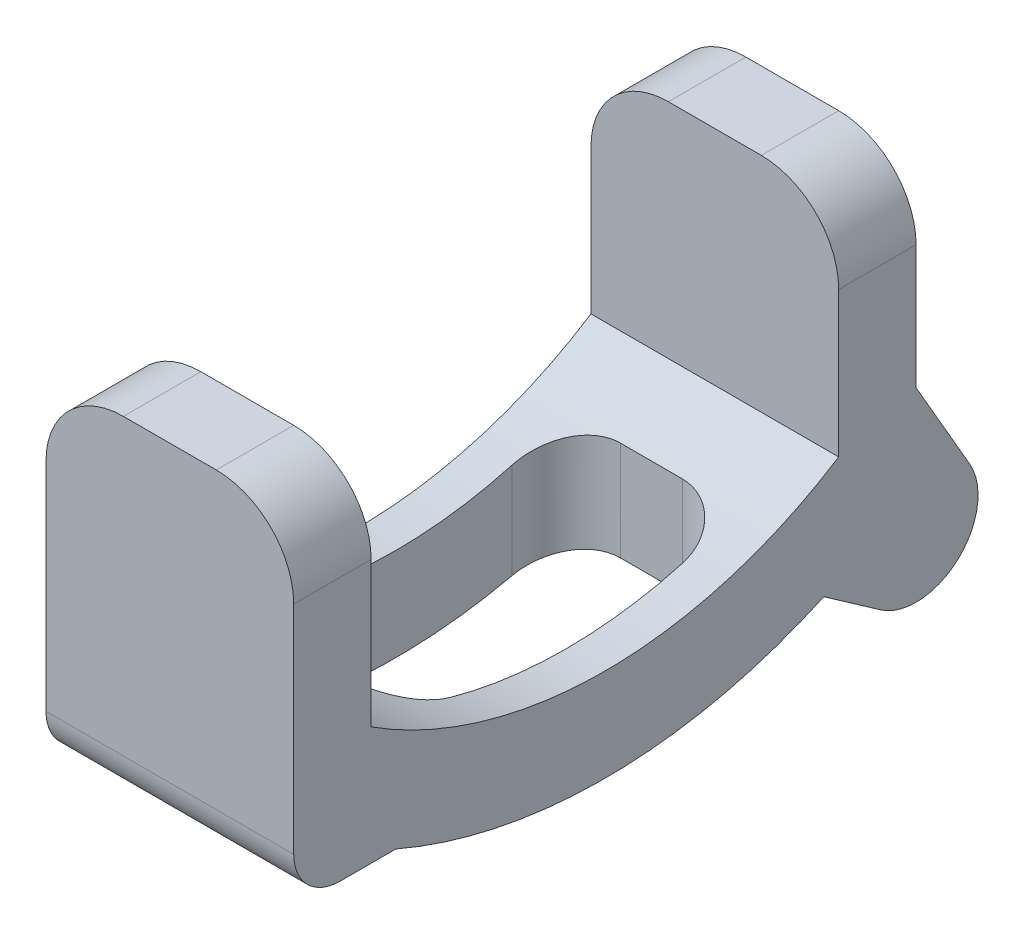
SolidWorks part; units mm, degrees
ref_plane "Přední rovina" through (0, 0, 0) normal (0, 0, 1) x (1, 0, 0)
ref_plane "Horní rovina" through (0, 0, 0) normal (0, 1, 0) x (1, 0, 0)
ref_plane "Pravá rovina" through (0, 0, 0) normal (1, 0, 0) x (0, 0, -1)
sketch "Skica1" plane through (0, 0, 0) normal (1, 0, 0) x (0, 0, -1)
  line L0 (-20.1, 0) -> (-20.1, 22)
  line L1 (-20.1, 22) -> (-15.1, 22)
  line L2 (-15.1, 22) -> (-15.1, 7.631)
  line L3 (0, 54.4876) -> (0, -54.4876) construction
  line L4 (-20.1, 0) -> (-13.5, 0)
  line L5 (14.1442, 0.2872) -> (17.8057, -2.2766)
  line L6 (15.1, 22) -> (15.1, 7.631)
  line L7 (20.1, 22) -> (15.1, 22)
  line L8 (20.1, 9) -> (20.1, 22)
  line L9 (23.5641, 3) -> (20.1, 9)
  arc A0 (-15.1, 7.631) -> (0, 3.2) centre (0, 31.1446) ccw
  arc A1 (-13.5, 0) -> (0, -2.8) centre (0, 31.1446) ccw
  arc A2 (14.1442, 0.2872) -> (0, -2.8) centre (0, 31.1446) cw
  arc A3 (15.1, 7.631) -> (0, 3.2) centre (0, 31.1446) cw
  arc A4 (17.8057, -2.2766) -> (23.5641, 3) centre (20.1, 1) ccw
  point P10 (0, 0)
  dimension "D3" = 6
  dimension "D4" = 4
  dimension "D1" = 5
  dimension "D2" = 40.2
  dimension "D5" = 25
  dimension "D6" = 22
  dimension "D7" = 150
  dimension "D8" = 6.6
  dimension "D9" = 18.8
  dimension "D10" = 25
extrude "Vysunout1" add sketch "Skica1" along normal mid plane 16
fillet "Zaoblit1" radius 5 4 edges at (-8, 22, -17.6) (8, 22, -17.6) (-8, 22, 17.6) (8, 22, 17.6)
fillet "Zaoblit2" radius 3 1 edges at (0, 0, 20.1)
ref_plane "Rovina1" through (0, 8, 0) normal (0, 1, 0) x (-1, 0, 0)
sketch "Skica2" plane through (0, 8, 0) normal (0, 1, 0) x (-1, 0, 0)
  line L0 (0, 0) -> (0, 9.2668) construction
  line L1 (5.5, 11) -> (-5.5, 11)
  line L2 (-5.5, 11) -> (-5.5, -11)
  line L3 (-8, 0) -> (8, 0) construction
  line L4 (-3.1955, 0) -> (10.7377, 0) construction
  line L5 (5.5, 11) -> (5.5, -11)
  line L6 (5.5, -11) -> (-5.5, -11)
  point P6 (0, -11)
  point P12 (0, 11)
  point P13 (5.5, 0)
  point P14 (-5.5, 0)
  dimension "D1" = 22
  dimension "D2" = 11
extrude "Odebrat vysunutím1" cut sketch "Skica2" against normal through all
fillet "Zaoblit3" radius 3.5 4 edges at (-5.5, 2.2439, -11) (5.5, 2.2439, -11) (-5.5, 2.2439, 11) (5.5, 2.2439, 11)
